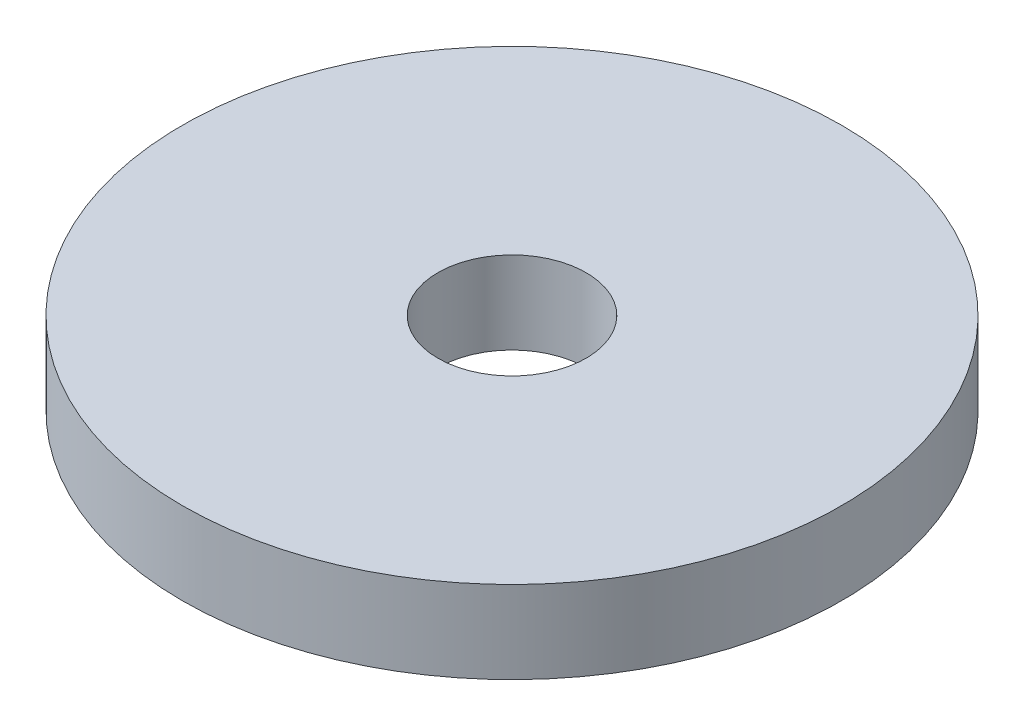
SolidWorks part; units mm, degrees
ref_plane "Front Plane" through (0, 0, 0) normal (0, 0, 1) x (1, 0, 0)
ref_plane "Top Plane" through (0, 0, 0) normal (0, 1, 0) x (1, 0, 0)
ref_plane "Right Plane" through (0, 0, 0) normal (1, 0, 0) x (0, 0, -1)
sketch "Sketch1" plane through (0, 0, 0) normal (0, 1, 0) x (1, 0, 0)
  circle A0 centre (0, 0) radius 20
  circle A1 centre (0, 0) radius 4.5
  dimension "D1" = 40
  dimension "D2" = 9
extrude "Boss-Extrude1" add sketch "Sketch1" against normal blind 5
